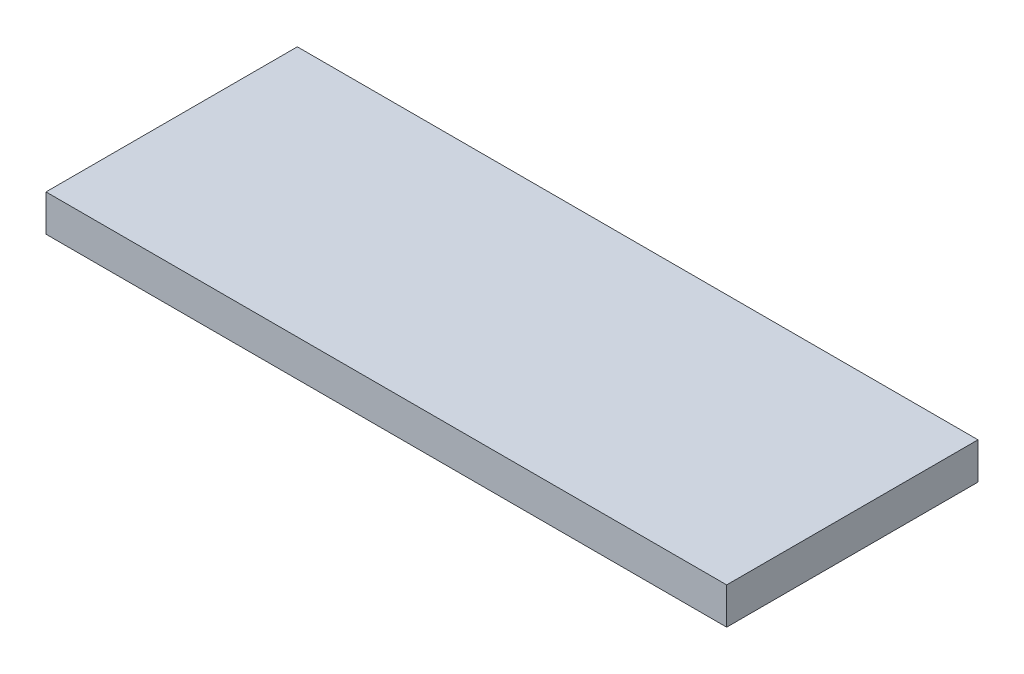
SolidWorks part; units mm, degrees
ref_plane "Front Plane" through (0, 0, 0) normal (0, 0, 1) x (1, 0, 0)
ref_plane "Top Plane" through (0, 0, 0) normal (0, 1, 0) x (1, 0, 0)
ref_plane "Right Plane" through (0, 0, 0) normal (1, 0, 0) x (0, 0, -1)
sketch "Sketch1" plane through (0, 0, 0) normal (0, 1, 0) x (1, 0, 0)
  line L1 (-162.5, -60) -> (162.5, -60)
  line L2 (-162.5, -60) -> (-162.5, 60)
  line L3 (-162.5, 60) -> (162.5, 60)
  line L4 (162.5, -60) -> (162.5, 60)
  point P4 (163.9137, 58.3937)
  point P5 (0, 60)
  point P7 (-162.5, 0)
  point P8 (162.5, 60)
  dimension "D1" = 325
  dimension "D2" = 120
extrude "Boss-Extrude1" add sketch "Sketch1" along normal blind 17.5
sketch "Sketch2" plane through (0, 17.5, 0) normal (0, 1, 0) x (1, 0, 0)
  line L0 (-162.5, 0) -> (162.5, 0) construction
  line L1 (-162.5, 60) -> (-162.5, -60) construction
  line L2 (162.5, -60) -> (162.5, 60) construction
  line L3 (0, 60) -> (0, -60) construction
  line L4 (162.5, 60) -> (-162.5, 60) construction
  line L5 (-162.5, -60) -> (162.5, -60) construction
  point P12 (0, 0)
